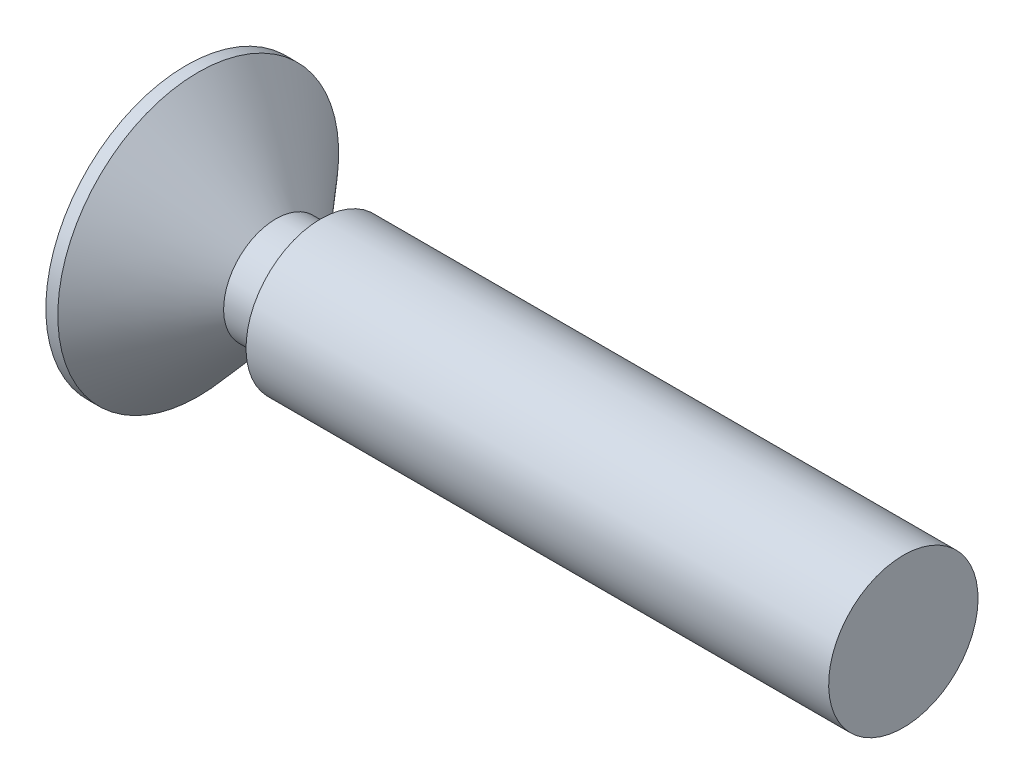
SolidWorks part; units mm, degrees
ref_plane "前视基准面" through (0, 0, 0) normal (0, 0, 1) x (1, 0, 0)
ref_plane "上视基准面" through (0, 0, 0) normal (0, 1, 0) x (1, 0, 0)
ref_plane "右视基准面" through (0, 0, 0) normal (1, 0, 0) x (0, 0, -1)
sketch "草图1" plane through (0, 0, 0) normal (0, 0, 1) x (1, 0, 0)
  line L0 (0, 0) -> (-43.2705, 0) construction
  line L1 (0, 0) -> (0, 1.25)
  line L2 (0, 1.25) -> (-9.75, 1.25)
  line L3 (-9.75, 1.25) -> (-9.75, 0.875)
  line L4 (-9.75, 0.875) -> (-10.5, 0.875)
  line L5 (-10.5, 0.875) -> (-11.8, 2.35)
  line L6 (-11.8, 2.35) -> (-12, 2.35)
  line L7 (-12, 2.35) -> (-12, 0)
  line L8 (-12, 0) -> (0, 0)
  dimension "D1" = 2.5
  dimension "D2" = 1.5
  dimension "D3" = 0.2
  dimension "D4" = 4.7
  dimension "D5" = 0.375
  dimension "D6" = 0.75
  dimension "D7" = 12
revolve "旋转1" add sketch "草图1" angle 360 about L0
cosmetic thread "装饰螺纹线1" parameters "D2"=2.15
sketch "草图2" plane through (-12, 0, 0) normal (-1, 0, 0) x (0, 0, 1)
  line L0 (1.5, 0) -> (-1.5, 0) construction
  line L1 (-0.3125, 1.5) -> (0.3125, 1.5)
  line L2 (-0.3125, 1.5) -> (-0.3125, 0.5625)
  line L3 (-0.3125, -1.5) -> (0.3125, -1.5)
  line L4 (0.3125, 1.5) -> (0.3125, 0.5625)
  line L5 (-1.5, 0.3125) -> (-0.5625, 0.3125)
  line L6 (-1.5, 0.3125) -> (-1.5, -0.3125)
  line L7 (-1.5, -0.3125) -> (-0.5625, -0.3125)
  line L8 (1.5, 0.3125) -> (1.5, -0.3125)
  line L9 (0, 1.5) -> (0, -1.5) construction
  line L10 (-0.3125, -0.5625) -> (-0.3125, -1.5)
  line L11 (0.5625, 0.3125) -> (1.5, 0.3125)
  line L12 (0.3125, -0.5625) -> (0.3125, -1.5)
  line L13 (0.5625, -0.3125) -> (1.5, -0.3125)
  arc A0 (-0.3125, -0.5625) -> (-0.5625, -0.3125) centre (-0.5625, -0.5625) ccw
  arc A1 (0.3125, -0.5625) -> (0.5625, -0.3125) centre (0.5625, -0.5625) cw
  arc A2 (0.5625, 0.3125) -> (0.3125, 0.5625) centre (0.5625, 0.5625) cw
  arc A3 (-0.3125, 0.5625) -> (-0.5625, 0.3125) centre (-0.5625, 0.5625) cw
  dimension "D3" = 0.25
  dimension "D1" = 0.625
  dimension "D2" = 3
extrude "切除-拉伸1" cut sketch "草图2" against normal blind 0.75
